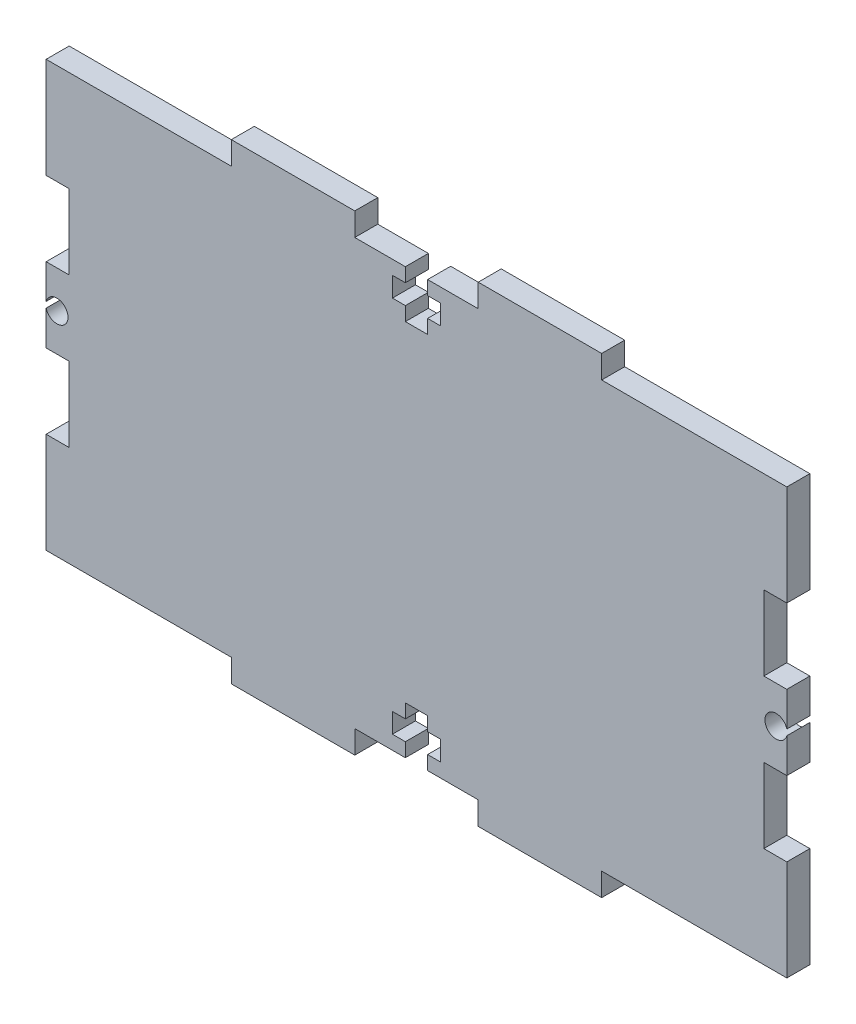
SolidWorks part; units mm, degrees
ref_plane "Front Plane" through (0, 0, 0) normal (0, 0, 1) x (1, 0, 0)
ref_plane "Top Plane" through (0, 0, 0) normal (0, 1, 0) x (1, 0, 0)
ref_plane "Right Plane" through (0, 0, 0) normal (1, 0, 0) x (0, 0, -1)
sketch "Sketch1" plane through (0, 0, 0) normal (0, 0, 1) x (1, 0, 0)
  line L1 (-48.26, 27.71) -> (48.26, 27.71)
  line L2 (-48.26, 27.71) -> (-48.26, -27.71)
  line L3 (-48.26, -27.71) -> (48.26, -27.71)
  line L4 (48.26, 27.71) -> (48.26, -27.71)
  line L5 (-48.26, 27.71) -> (48.26, -27.71) construction
  line L6 (-48.26, -27.71) -> (48.26, 27.71) construction
  point P0 (0, 0)
  dimension "D1" = 96.52
  dimension "D2" = 55.42
extrude "Boss-Extrude1" add sketch "Sketch1" along normal blind 3
sketch "Sketch2" plane through (0, 27.71, 0) normal (0, 1, 0) x (1, 0, 0)
  line L5 (48.26, -3) -> (-48.26, -3) construction
  line L6 (48.26, 0) -> (-48.26, 0) construction
  line L11 (-24.13, 0) -> (24.13, 0)
  line L12 (-24.13, 0) -> (-24.13, -3)
  line L13 (-24.13, -3) -> (24.13, -3)
  line L14 (24.13, 0) -> (24.13, -3)
  point P4 (0, 0)
  point P5 (0, 0)
  dimension "D1" = 48.26
extrude "Boss-Extrude2" add sketch "Sketch2" along normal blind 3
mirror "Mirror1" about plane through (0, 0, 0) normal (0, 1, 0) of "Boss-Extrude2"
sketch "Sketch4" plane through (48.26, 0, 0) normal (1, 0, 0) x (0, 0, -1)
  line L5 (-3, -27.71) -> (-3, 27.71) construction
  line L6 (0, -27.71) -> (0, 27.71) construction
  line L11 (-3, -14.605) -> (0, -14.605)
  line L12 (-3, -14.605) -> (-3, 14.605)
  line L13 (-3, 14.605) -> (0, 14.605)
  line L14 (0, -14.605) -> (0, 14.605)
  point P4 (0, 0)
  point P5 (0, 0)
  dimension "D1" = 29.21
extrude "Cut-Extrude1" cut sketch "Sketch4" against normal blind 3
mirror "Mirror2" about plane through (0, 0, 0) normal (1, 0, 0) of "Cut-Extrude1"
sketch "Sketch5" plane through (0, 30.71, 0) normal (0, 1, 0) x (1, 0, 0)
  line L0 (-24.13, -3) -> (24.13, -3) construction
  line L1 (-8.0433, -3) -> (8.0433, -3)
  line L2 (-8.0433, -3) -> (-8.0433, 0)
  line L3 (-8.0433, 0) -> (8.0433, 0)
  line L4 (8.0433, -3) -> (8.0433, 0)
  point P6 (0, 0)
  dimension "D1" = 16.0867
extrude "Cut-Extrude2" cut sketch "Sketch5" against normal blind 3
mirror "Mirror3" about plane through (0, 0, 0) normal (0, 1, 0) of "Cut-Extrude2"
sketch "Sketch6" plane through (-45.26, 0, 0) normal (-1, 0, 0) x (0, 0, 1)
  line L0 (0, -14.605) -> (0, 14.605) construction
  line L1 (0, 4.869) -> (3, 4.869)
  line L2 (0, 4.869) -> (0, -4.869)
  line L3 (0, -4.869) -> (3, -4.869)
  line L4 (3, 4.869) -> (3, -4.869)
  line L5 (3, 14.605) -> (3, -14.605) construction
  point P6 (3, 0)
  point P9 (3, 0)
  dimension "D1" = 9.7379
extrude "Boss-Extrude3" add sketch "Sketch6" along normal blind 3
mirror "Mirror4" about plane through (0, 0, 0) normal (1, 0, 0) of "Boss-Extrude3"
sketch "Sketch7" plane through (0, -27.71, 0) normal (0, -1, 0) x (1, 0, 0)
  line L0 (-8.0433, 3) -> (8.0433, 3) construction
  line L1 (1.45, 0) -> (-1.45, 0)
  line L2 (1.45, 0) -> (1.45, 3)
  line L3 (1.45, 3) -> (-1.45, 3)
  line L4 (-1.45, 0) -> (-1.45, 3)
  line L5 (8.0433, 0) -> (-8.0433, 0) construction
  point P6 (0, 0)
  point P9 (0, 0)
  dimension "D1" = 2.9
extrude "Cut-Extrude3" cut sketch "Sketch7" against normal blind 6.2
sketch "Sketch9" plane through (0, 0, 0) normal (0, 0, -1) x (-1, 0, 0)
  line L0 (1.45, -21.51) -> (1.45, -27.71) construction
  line L1 (3.135, -25.8968) -> (-3.135, -25.8968)
  line L2 (3.135, -25.8968) -> (3.135, -23.3232)
  line L3 (3.135, -23.3232) -> (-3.135, -23.3232)
  line L4 (-3.135, -25.8968) -> (-3.135, -23.3232)
  line L5 (1.45, -21.51) -> (-1.45, -21.51) construction
  point P6 (1.45, -24.61)
  point P7 (3.135, -24.61)
  point P8 (0, -23.3232)
  point P11 (0, -21.51)
  dimension "D1" = 6.27
extrude "Cut-Extrude4" cut sketch "Sketch9" against normal blind 3
mirror "Mirror5" about plane through (0, 0, 0) normal (0, 1, 0) of "Cut-Extrude3"
mirror "Mirror6" about plane through (0, 0, 0) normal (0, 1, 0) of "Cut-Extrude4"
sketch "Sketch10" plane through (0, 0, 0) normal (0, 0, -1) x (-1, 0, 0)
  line L0 (48.26, 4.869) -> (48.26, -4.869) construction
  line L1 (48.31, -1.4934) -> (45.31, -1.4934)
  line L2 (48.31, -1.4934) -> (48.31, 1.5066)
  line L3 (48.31, 1.5066) -> (45.31, 1.5066)
  line L4 (45.31, -1.4934) -> (45.31, 1.5066)
  circle A0 centre (46.86, 0.0066) radius 1.45
  point P7 (48.31, 0.0066)
  dimension "D3" = 2.9
  dimension "D1" = 3
  dimension "D2" = 3
  dimension "D4" = 0.05
extrude "Cut-Extrude5" cut sketch "Sketch10" against normal blind 3 contours A0
mirror "Mirror7" about plane through (0, 0, 0) normal (1, 0, 0) of "Cut-Extrude5"
